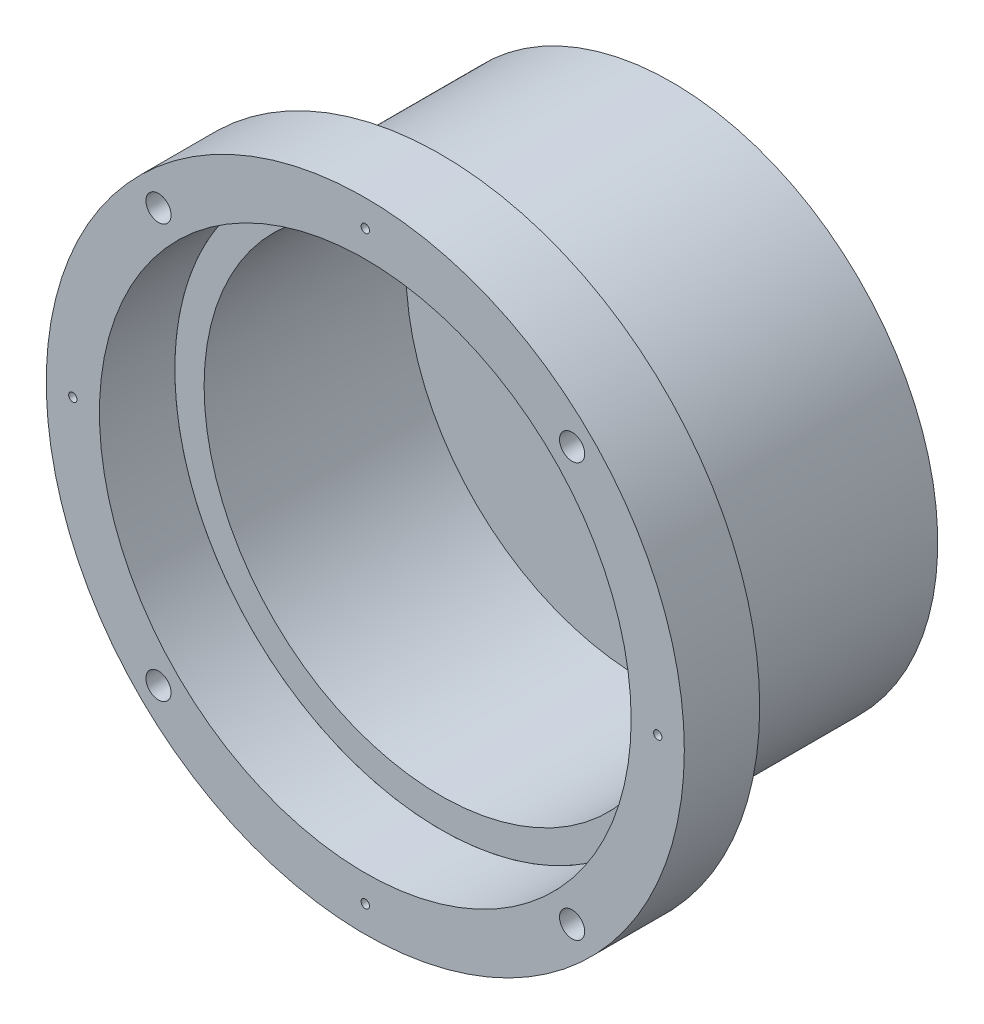
SolidWorks part; units mm, degrees
ref_plane "Front Plane" through (0, 0, 0) normal (0, 0, 1) x (1, 0, 0)
ref_plane "Top Plane" through (0, 0, 0) normal (0, 1, 0) x (1, 0, 0)
ref_plane "Right Plane" through (0, 0, 0) normal (1, 0, 0) x (0, 0, -1)
sketch "Sketch1" plane through (0, 0, 0) normal (0, 0, 1) x (1, 0, 0)
  line L0 (0, 70.5725) -> (0, 76.2) construction
  line L3 (-1.25, 69.3225) -> (12.2983, 69.3225) construction
  circle A0 centre (0, 0) radius 63.5
  circle A1 centre (0, 0) radius 76.2
  circle A2 centre (0, 69.3225) radius 1.25 construction
  circle A3 centre (69.3225, 0) radius 1.25 construction
  circle A4 centre (0, -69.3225) radius 1.25 construction
  circle A5 centre (-69.3225, 0) radius 1.25 construction
  point P19 (0, 0)
  dimension "D1" = 127
  dimension "D2" = 152.4
  dimension "D3" = 2.5
  dimension "D5" = 5.6275
  dimension "D4" = 4
extrude "Boss-Extrude1" add sketch "Sketch1" along normal blind 28.225
sketch "Sketch2" plane through (0, 0, 0) normal (0, 0, -1) x (-1, 0, 0)
  circle A0 centre (0, 69.3225) radius 2.5
  circle A1 centre (69.3225, 0) radius 2.5
  circle A2 centre (0, -69.3225) radius 2.5
  circle A3 centre (-69.3225, 0) radius 2.5
  point P12 (0, 0)
  dimension "D1" = 5
  dimension "D2" = 4
extrude "Cut-Extrude1" [suppressed] cut sketch "Sketch2" against normal blind 6.725
sketch "Sketch3" plane through (0, 0, 28.225) normal (0, 0, 1) x (1, 0, 0)
  line L0 (0, 69.3225) -> (0, 0) construction
  line L1 (0, 0) -> (-79.0122, 79.0122) construction
  line L2 (-53.8815, 53.8815) -> (-53.8815, 44.9013) construction
  line L3 (-53.8815, 44.9013) -> (-44.9013, 44.9013) construction
  line L4 (-53.8815, 44.9013) -> (-46.9345, 51.8484) construction
  circle A0 centre (0, 0) radius 76.2 construction
  circle A1 centre (0, 0) radius 63.5 construction
  circle A2 centre (-49.3914, 49.3914) radius 3
  circle A3 centre (49.3914, 49.3914) radius 3
  circle A4 centre (49.3914, -49.3914) radius 3
  circle A5 centre (-49.3914, -49.3914) radius 3
  point P25 (0, 0)
  dimension "D2" = 6
  dimension "D1" = 45
  dimension "D3" = 4
extrude "Cut-Extrude2" cut sketch "Sketch3" against normal through all
sketch "Sketch4" plane through (0, 0, 28.225) normal (0, 0, 1) x (1, 0, 0)
  circle A0 centre (0, 0) radius 107.9579
extrude "Cut-Extrude3" cut sketch "Sketch4" against normal blind 10.225
sketch "Sketch5" plane through (0, 0, 0) normal (0, 0, -1) x (-1, 0, 0)
  circle A0 centre (0, 0) radius 63.5
  circle A1 centre (0, 0) radius 56.5
  circle A2 centre (0, 0) radius 63.5 construction
  dimension "D1" = 7
extrude "Boss-Extrude2" add sketch "Sketch5" along normal blind 55.225 separate body
sketch "Sketch6" plane through (0, 0, -55.225) normal (0, 0, -1) x (-1, 0, 0)
  circle A0 centre (0, 0) radius 56.5
extrude "Boss-Extrude3" add sketch "Sketch6" against normal blind 7
sketch "Sketch7" plane through (0, 0, 0) normal (0, 0, -1) x (-1, 0, 0)
  line L0 (0, 76.2) -> (0, 63.5) construction
  line L1 (0, 63.5) -> (-8.1249, 69.85) construction
  line L2 (-8.1249, 69.85) -> (0, 76.2) construction
  line L3 (-8.1249, 69.85) -> (0, 69.85) construction
  circle A0 centre (0, 69.85) radius 2
  circle A1 centre (0, 0) radius 76.2 construction
  circle A2 centre (0, 0) radius 63.5 construction
  circle A3 centre (69.85, 0) radius 2
  circle A4 centre (0, -69.85) radius 2
  circle A5 centre (-69.85, 0) radius 2
  point P20 (0, 0)
  dimension "D1" = 4
  dimension "D2" = 4
extrude "Cut-Extrude4" cut sketch "Sketch7" against normal blind 10
sketch "Sketch8" plane through (0, 0, 0) normal (0, 0, -1) x (-1, 0, 0)
  circle A0 centre (0, 69.85) radius 1
  circle A1 centre (69.85, 0) radius 1
  circle A2 centre (0, -69.85) radius 1
  circle A3 centre (-69.85, 0) radius 1
  point P12 (0, 0)
  dimension "D1" = 2
  dimension "D2" = 4
extrude "Cut-Extrude5" cut sketch "Sketch8" against normal through all
